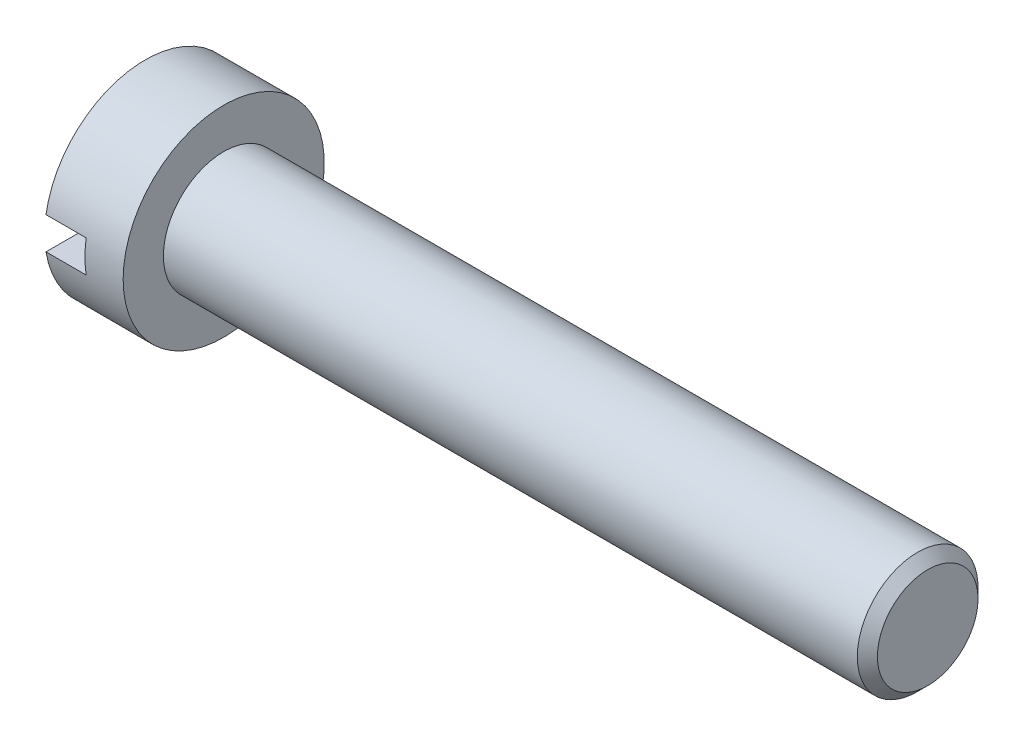
SolidWorks part; units mm, degrees
ref_plane "Plan de face" through (0, 0, 0) normal (0, 0, 1) x (1, 0, 0)
ref_plane "Plan de dessus" through (0, 0, 0) normal (0, 1, 0) x (1, 0, 0)
ref_plane "Plan de droite" through (0, 0, 0) normal (1, 0, 0) x (0, 0, -1)
sketch "Esquisse1" plane through (0, 0, 0) normal (0, 0, 1) x (1, 0, 0)
  line L0 (0, 3) -> (0, 5)
  line L1 (0, 5) -> (-3.9, 5)
  line L2 (-3.9, 5) -> (-3.9, 0)
  line L3 (-3.9, 0) -> (35, 0)
  line L4 (35, 0) -> (35, 2.5)
  line L5 (35, 2.5) -> (34.5, 3)
  line L6 (34.5, 3) -> (0, 3)
  dimension "D1" = 3.9
  dimension "D2" = 35
  dimension "D3" = 0.5
  dimension "D4" = 0.5
  dimension "D5" = 3
  dimension "D6" = 5
revolve "Révolution1" add sketch "Esquisse1" angle 360 about L3
cosmetic thread "Représentation de filetage1" parameters "D1"=35, "D2"=4.891
sketch "Esquisse2" plane through (-3.9, 0, 0) normal (-1, 0, 0) x (0, 0, 1)
  line L1 (-6, 0.8) -> (6, 0.8)
  line L2 (-6, 0.8) -> (-6, -0.8)
  line L3 (-6, -0.8) -> (6, -0.8)
  line L4 (6, 0.8) -> (6, -0.8)
  dimension "D1" = 6
  dimension "D2" = 6
  dimension "D3" = 0.8
  dimension "D4" = 0.8
extrude "Enlèv. mat.-Extru.1" cut sketch "Esquisse2" against normal blind 2
